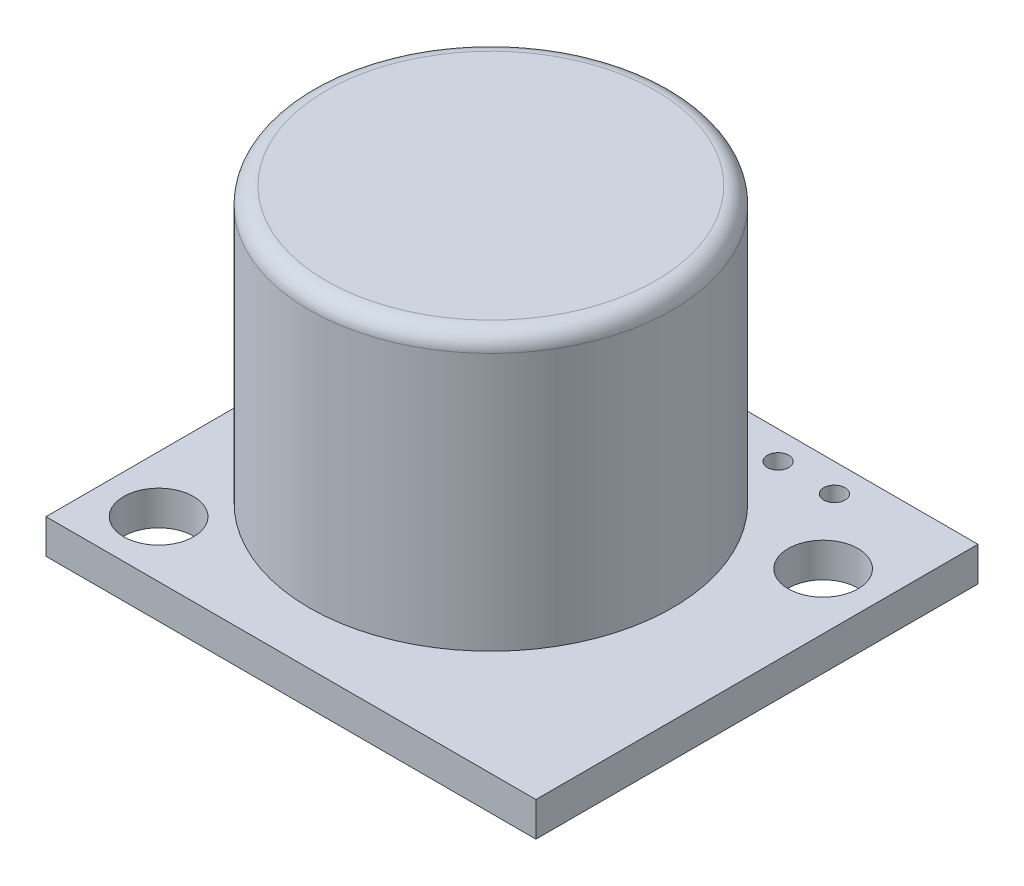
SolidWorks part; units mm, degrees
ref_plane "Front Plane" through (0, 0, 0) normal (0, 0, 1) x (1, 0, 0)
ref_plane "Top Plane" through (0, 0, 0) normal (0, 1, 0) x (1, 0, 0)
ref_plane "Right Plane" through (0, 0, 0) normal (1, 0, 0) x (0, 0, -1)
sketch "Sketch2" plane through (0, 0, 0) normal (0, 1, 0) x (1, 0, 0)
  line L1 (0, 0) -> (22.098, 0)
  line L2 (0, 0) -> (0, 19.939)
  line L3 (0, 19.939) -> (22.098, 19.939)
  line L4 (22.098, 0) -> (22.098, 19.939)
  dimension "D1" = 19.939
  dimension "D2" = 22.098
extrude "Boss-Extrude1" add sketch "Sketch2" along normal blind 1.5494
sketch "Sketch6" plane through (0, 1.5494, 0) normal (0, 1, 0) x (1, 0, 0)
  line L0 (0, 19.939) -> (11.049, 19.939)
  line L1 (22.098, 19.939) -> (0, 19.939) construction
  line L2 (11.049, 19.939) -> (11.049, 0)
  line L3 (0, 0) -> (22.098, 0) construction
  line L4 (11.049, 0) -> (11.049, 9.017)
  circle A0 centre (11.049, 9.017) radius 5.08
  dimension "D2" = 10.16
  dimension "D1" = 9.017
extrude "Boss-Extrude3" add sketch "Sketch6" along normal blind 1.5494 contours L2 A0 | L2 A0
sketch "Sketch7" plane through (0, 3.0988, 0) normal (0, 1, 0) x (1, 0, 0)
  circle A0 centre (11.049, 9.017) radius 8.1915
  dimension "D1" = 16.383
extrude "Boss-Extrude4" add sketch "Sketch7" along normal blind 12.3952
sketch "Sketch8" plane through (0, 1.5494, 0) normal (0, 1, 0) x (1, 0, 0)
  line L0 (0, 0) -> (2.54, 0)
  line L1 (0, 0) -> (22.098, 0) construction
  line L2 (2.54, 0) -> (2.54, 2.54)
  line L3 (2.54, 2.54) -> (19.558, 2.54)
  line L4 (19.558, 2.54) -> (19.558, 15.494)
  line L5 (0, 0) -> (0, 18.669)
  line L6 (0, 19.939) -> (0, 0) construction
  line L7 (0, 18.669) -> (1.651, 18.669)
  line L8 (1.651, 18.669) -> (4.191, 18.669)
  line L9 (4.191, 18.669) -> (6.731, 18.669)
  line L10 (6.731, 18.669) -> (9.271, 18.669)
  line L11 (9.271, 18.669) -> (11.811, 18.669)
  line L12 (11.811, 18.669) -> (14.351, 18.669)
  line L13 (14.351, 18.669) -> (16.891, 18.669)
  circle A0 centre (2.54, 2.54) radius 1.5748
  circle A1 centre (19.558, 15.494) radius 1.5748
  circle A2 centre (16.891, 18.669) radius 0.4826
  circle A3 centre (14.351, 18.669) radius 0.4826
  circle A4 centre (11.811, 18.669) radius 0.4826
  circle A5 centre (9.271, 18.669) radius 0.4826
  circle A6 centre (6.731, 18.669) radius 0.4826
  circle A7 centre (4.191, 18.669) radius 0.4826
  circle A8 centre (1.651, 18.669) radius 0.4826
  dimension "D3" = 3.1496
  dimension "D6" = 3.1496
  dimension "D15" = 0.9652
  dimension "D16" = 0.9652
  dimension "D17" = 0.9652
  dimension "D18" = 0.9652
  dimension "D19" = 0.9652
  dimension "D20" = 0.9652
  dimension "D21" = 0.9652
  dimension "D1" = 2.54
  dimension "D2" = 2.54
  dimension "D4" = 17.018
  dimension "D5" = 12.954
  dimension "D7" = 18.669
  dimension "D8" = 1.651
  dimension "D9" = 2.54
  dimension "D10" = 2.54
  dimension "D11" = 2.54
  dimension "D12" = 2.54
  dimension "D13" = 2.54
  dimension "D14" = 2.54
extrude "Cut-Extrude1" cut sketch "Sketch8" against normal through all
fillet "Fillet1" radius 0.762 1 edges at (11.049, 15.494, -0.8255)
